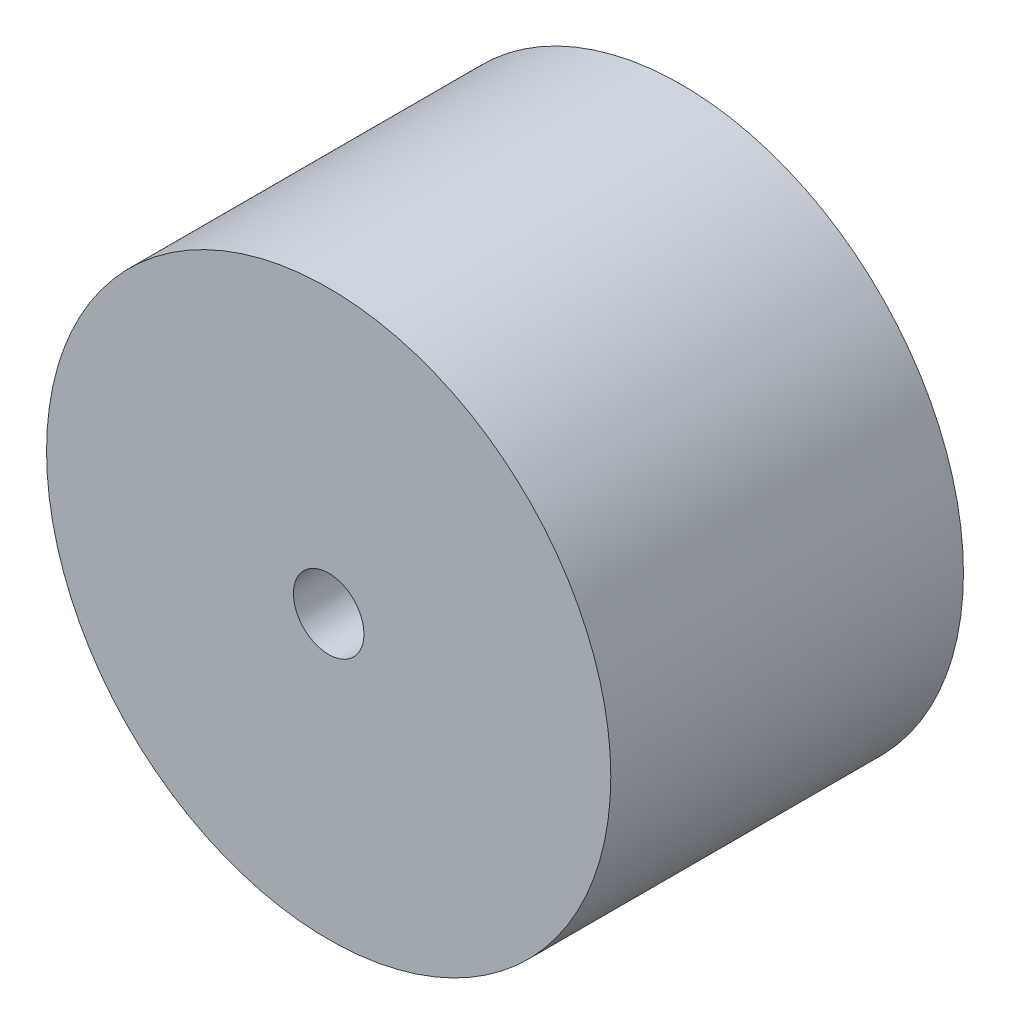
SolidWorks part; units mm, degrees
ref_plane "Front Plane" through (0, 0, 0) normal (0, 0, 1) x (1, 0, 0)
ref_plane "Top Plane" through (0, 0, 0) normal (0, 1, 0) x (1, 0, 0)
ref_plane "Right Plane" through (0, 0, 0) normal (1, 0, 0) x (0, 0, -1)
sketch "Sketch1" plane through (0, 0, 0) normal (0, 0, 1) x (1, 0, 0)
  circle A0 centre (0, 0) radius 5
  circle A1 centre (0, 0) radius 40
  dimension "D1" = 10
  dimension "D2" = 80
extrude "Boss-Extrude1" add sketch "Sketch1" along normal blind 50
